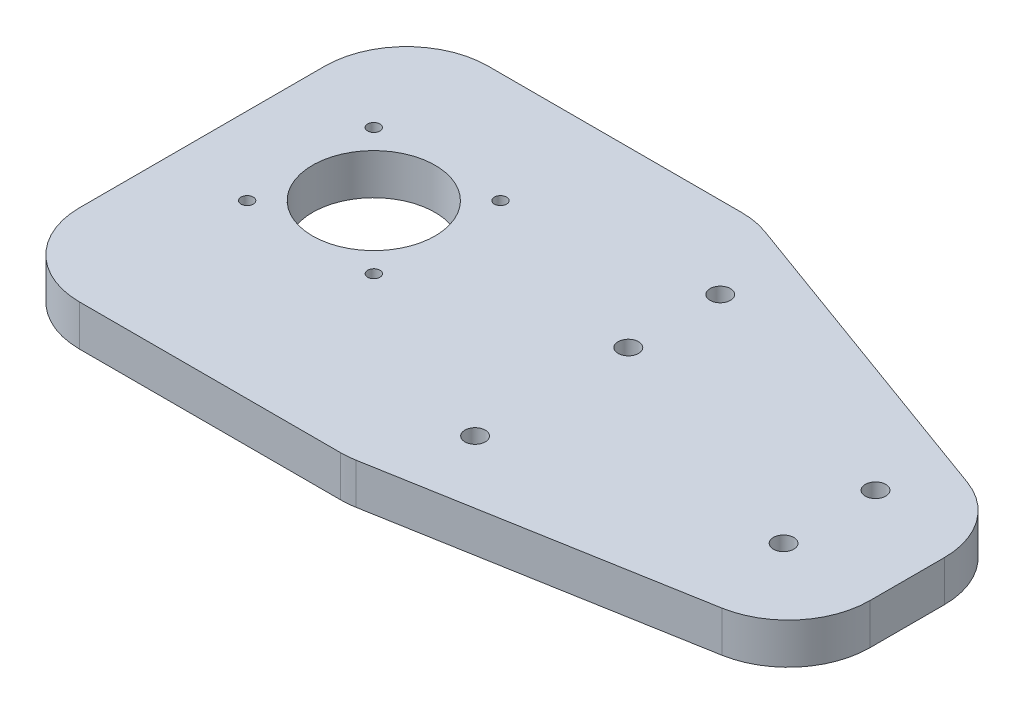
SolidWorks part; units mm, degrees
ref_plane "Front Plane" through (0, 0, 0) normal (0, 0, 1) x (1, 0, 0)
ref_plane "Top Plane" through (0, 0, 0) normal (0, 1, 0) x (1, 0, 0)
ref_plane "Right Plane" through (0, 0, 0) normal (1, 0, 0) x (0, 0, -1)
sketch "Sketch2" plane through (0, 0, 0) normal (0, 1, 0) x (1, 0, 0)
  line L0 (0, 20) -> (0, 80)
  line L1 (20, 100) -> (82.081, 100)
  line L2 (88.9214, 98.7939) -> (166.8404, 70.4336)
  line L3 (180, 51.6398) -> (180, 33.4259)
  line L4 (163.473, 13.7298) -> (87.3307, 0.3038)
  line L5 (83.8577, 0) -> (20, 0)
  line L6 (96.8, 80) -> (96.8, 35) construction
  line L7 (34.5, 75.2459) -> (34.5, 37.6789) construction
  line L8 (13.5, 36.5) -> (55.5, 36.5)
  line L9 (13.5, 36.5) -> (13.5, 78.5)
  line L10 (13.5, 78.5) -> (55.5, 78.5)
  line L11 (55.5, 36.5) -> (55.5, 78.5)
  line L12 (13.5, 36.5) -> (55.5, 78.5) construction
  line L13 (13.5, 78.5) -> (55.5, 36.5) construction
  line L14 (17.1358, 57.5) -> (53.2071, 57.5) construction
  circle A0 centre (96.8, 80) radius 2.5
  circle A1 centre (96.8, 20) radius 2.5
  circle A2 centre (157.3, 35) radius 2.5
  circle A3 centre (34.5, 57.5) radius 15
  arc A4 (82.081, 100) -> (88.9214, 98.7939) centre (82.081, 80) cw
  arc A5 (166.8404, 70.4336) -> (180, 51.6398) centre (160, 51.6398) cw
  arc A6 (180, 33.4259) -> (163.473, 13.7298) centre (160, 33.4259) cw
  arc A7 (87.3307, 0.3038) -> (83.8577, 0) centre (83.8577, 20) cw
  arc A8 (0, 20) -> (20, 0) centre (20, 20) ccw
  arc A9 (0, 80) -> (20, 100) centre (20, 80) cw
  circle A10 centre (19, 73) radius 1.5
  circle A13 centre (50, 73) radius 1.5
  circle A14 centre (19, 42) radius 1.5
  circle A15 centre (50, 42) radius 1.5
  circle A16 centre (96.8, 57.5) radius 2.5
  circle A17 centre (157.3, 57.5) radius 2.5
  point P18 (96.8, 57.5)
  point P24 (85.6075, 100)
  point P27 (180, 65.6439)
  point P30 (180, 16.6439)
  point P33 (85.6075, 0)
  point P36 (0, 0)
  point P39 (0, 100)
  dimension "D8" = 30
  dimension "D12" = 41.3
  dimension "D14" = 5
  dimension "D15" = 5
  dimension "D16" = 5
  dimension "D19" = 20
  dimension "D21" = 3
  dimension "D22" = 5
  dimension "D23" = 5
  dimension "D1" = 100
  dimension "D2" = 60
  dimension "D3" = 20
  dimension "D4" = 45
  dimension "D5" = 60.5
  dimension "D6" = 10
  dimension "D7" = 20
  dimension "D9" = 45
  dimension "D10" = 42
  dimension "D11" = 42
  dimension "D13" = 13.5
  dimension "D17" = 49
  dimension "D18" = 180
  dimension "D20" = 15.5
extrude "Boss-Extrude1" add sketch "Sketch2" along normal blind 10 contours A9 L0 A8 L5 A7 L4 A6 L3 A5 L2 A4 L1 A2 A1 A0 L11 L8 L9 L10 | L8 L11 L10 L9 A15 A13 A10 A3 A14
